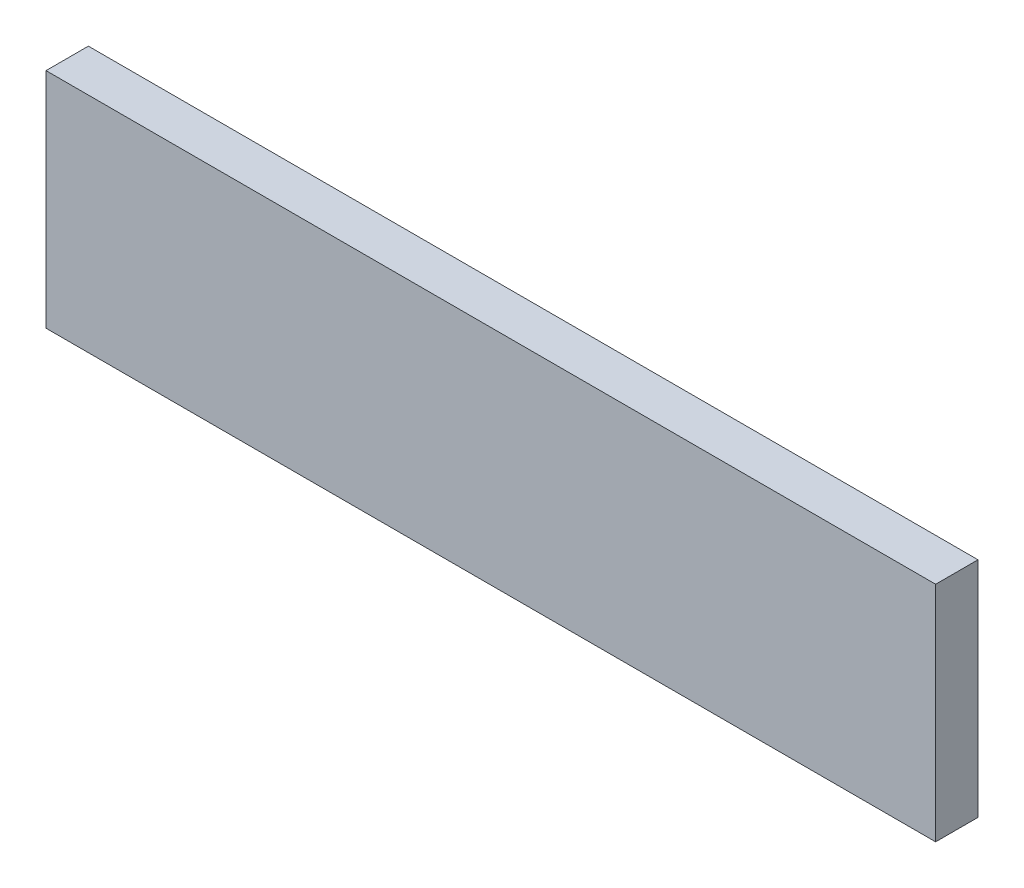
SolidWorks part; units mm, degrees
ref_plane "Front Plane" through (0, 0, 0) normal (0, 0, 1) x (1, 0, 0)
ref_plane "Top Plane" through (0, 0, 0) normal (0, 1, 0) x (1, 0, 0)
ref_plane "Right Plane" through (0, 0, 0) normal (1, 0, 0) x (0, 0, -1)
sketch "Sketch1" plane through (0, 0, 0) normal (0, 0, 1) x (1, 0, 0)
  line L1 (-40.005, -10.033) -> (40.005, -10.033)
  line L2 (-40.005, -10.033) -> (-40.005, 10.033)
  line L3 (-40.005, 10.033) -> (40.005, 10.033)
  line L4 (40.005, -10.033) -> (40.005, 10.033)
  line L5 (-40.005, -10.033) -> (40.005, 10.033) construction
  line L6 (-40.005, 10.033) -> (40.005, -10.033) construction
  point P0 (0, 0)
  dimension "D1" = 80.01
  dimension "D2" = 20.066
extrude "Boss-Extrude1" add sketch "Sketch1" along normal blind 3.81
